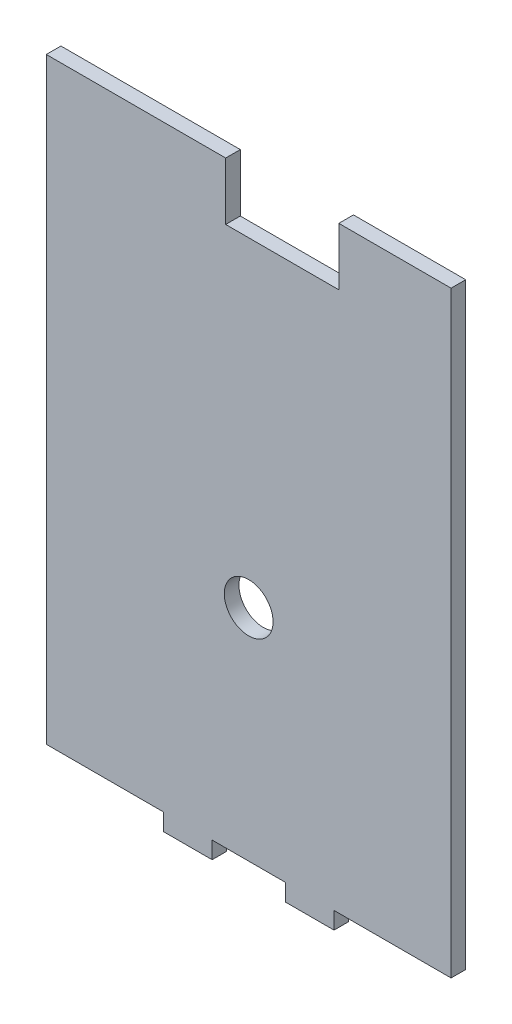
SolidWorks part; units mm, degrees
ref_plane "Alzado" through (0, 0, 0) normal (0, 0, 1) x (1, 0, 0)
ref_plane "Planta" through (0, 0, 0) normal (0, 1, 0) x (1, 0, 0)
ref_plane "Vista lateral" through (0, 0, 0) normal (1, 0, 0) x (0, 0, -1)
sketch "Model" plane through (0, 0, 0) normal (0, 0, 1) x (1, 0, 0)
  line L0 (81.1212, 81.8215) -> (70.1118, 81.8215)
  line L1 (70.1118, 81.8215) -> (58.1024, 81.8215)
  line L2 (58.1024, 81.8215) -> (58.1024, 70.0215)
  line L3 (58.1024, 70.0215) -> (34.9024, 70.0215)
  line L4 (34.9024, 70.0215) -> (34.9024, 81.8215)
  line L5 (34.9024, 81.8215) -> (19.6947, 81.8215)
  line L7 (19.6947, 81.8215) -> (-1.8788, 81.8215)
  line L9 (-1.8788, 81.8215) -> (-1.8788, -40.6785)
  line L10 (22.1212, -40.6785) -> (-1.8788, -40.6785)
  line L11 (22.1212, -44.1785) -> (22.1212, -40.6785)
  line L12 (32.1212, -44.1785) -> (22.1212, -44.1785)
  line L13 (32.1212, -40.6785) -> (32.1212, -44.1785)
  line L14 (47.1212, -40.6785) -> (32.1212, -40.6785)
  line L15 (47.1212, -44.1785) -> (47.1212, -40.6785)
  line L16 (57.1212, -44.1785) -> (47.1212, -44.1785)
  line L17 (57.1212, -40.6785) -> (57.1212, -44.1785)
  line L18 (81.1212, -40.6785) -> (57.1212, -40.6785)
  line L19 (81.1212, 81.8215) -> (81.1212, -40.6785)
  circle A0 centre (39.6212, 4.3215) radius 5
extrude "Saliente-Extruir1" add sketch "Model" along normal blind 3
